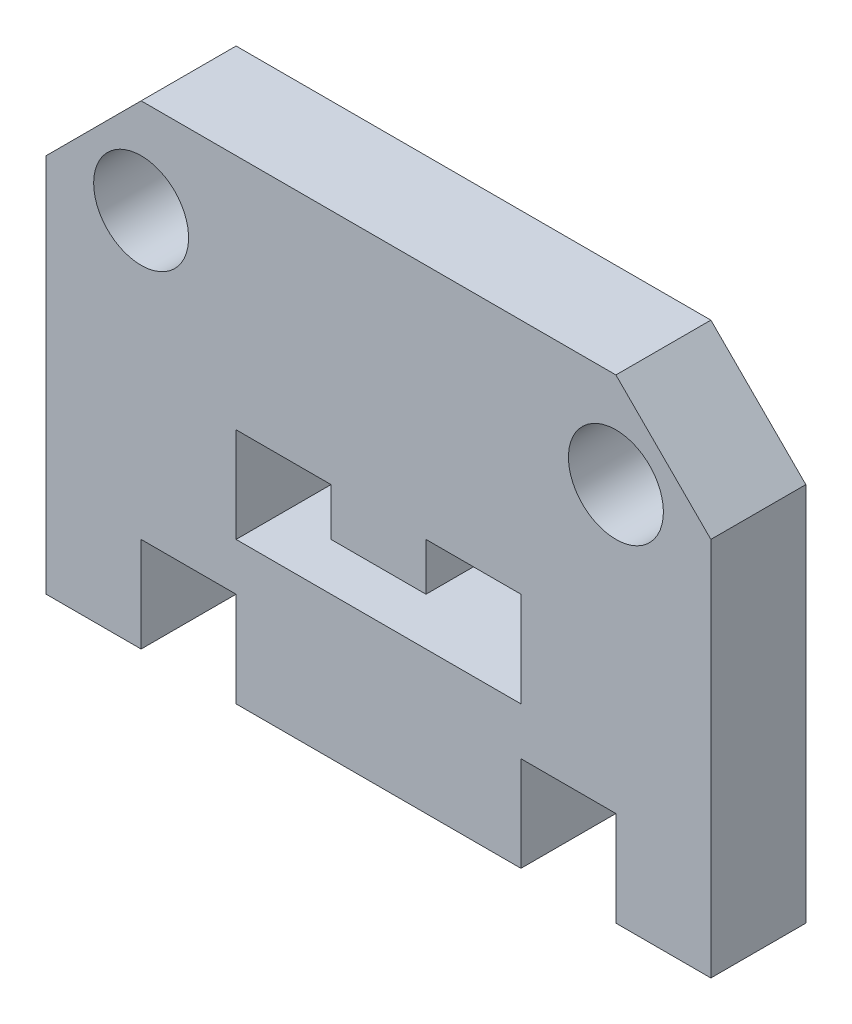
SolidWorks part; units mm, degrees
ref_plane "Front Plane" through (0, 0, 0) normal (0, 0, 1) x (1, 0, 0)
ref_plane "Top Plane" through (0, 0, 0) normal (0, 1, 0) x (1, 0, 0)
ref_plane "Right Plane" through (0, 0, 0) normal (1, 0, 0) x (0, 0, -1)
sketch "Sketch1" plane through (0, 0, 0) normal (0, 0, 1) x (1, 0, 0)
  line L0 (0, -26.0049) -> (0, -59.4771) construction
  line L1 (-15, 0) -> (15, 0)
  line L2 (15, 0) -> (15, 10)
  line L3 (15, 10) -> (25, 10)
  line L4 (25, 10) -> (25, 0)
  line L5 (25, 0) -> (35, 0)
  line L6 (35, 0) -> (35, 40)
  line L7 (35, 40) -> (25, 50)
  line L8 (25, 50) -> (-25, 50)
  line L9 (-5, 20) -> (5, 20)
  line L10 (5, 20) -> (5, 25)
  line L11 (5, 25) -> (15, 25)
  line L12 (15, 25) -> (15, 15)
  line L13 (15, 15) -> (-15, 15)
  line L14 (35, 40) -> (35, 59.2138) construction
  line L15 (-25, 0) -> (-35, 0)
  line L16 (-25, 10) -> (-25, 0)
  line L17 (-15, 0) -> (-15, 10)
  line L18 (-15, 10) -> (-25, 10)
  line L19 (-5, 25) -> (-15, 25)
  line L20 (-5, 20) -> (-5, 25)
  line L21 (-15, 25) -> (-15, 15)
  line L22 (-35, 0) -> (-35, 40)
  line L23 (-35, 40) -> (-25, 50)
  circle A0 centre (25, 40) radius 5
  circle A1 centre (-25, 40) radius 5
  point P10 (0, 0)
  point P21 (0, 0)
  point P22 (0, 0)
  point P23 (0, 0)
  point P24 (0, 0)
  point P25 (0, 0)
  point P31 (0, 0)
  point P35 (0, 20)
  point P36 (0, 15)
  point P40 (0, 50)
  dimension "D9" = 10
  dimension "D1" = 50
  dimension "D2" = 10
  dimension "D3" = 5
  dimension "D4" = 15
  dimension "D5" = 30
  dimension "D6" = 20
  dimension "D7" = 45
  dimension "D8" = 10
  dimension "D10" = 40
  dimension "D11" = 10
  dimension "D12" = 10
  dimension "D13" = 10
  dimension "D14" = 10
extrude "Boss-Extrude1" add sketch "Sketch1" along normal blind 10
